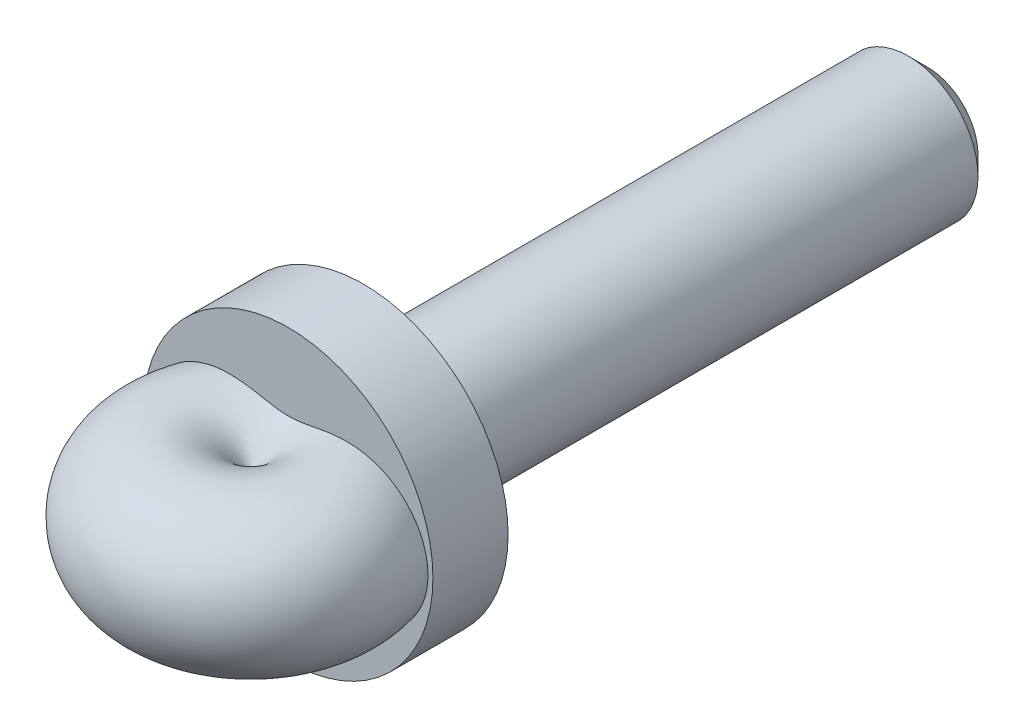
SolidWorks part; units mm, degrees
ref_plane "Front Plane" through (0, 0, 0) normal (0, 0, 1) x (1, 0, 0)
ref_plane "Top Plane" through (0, 0, 0) normal (0, 1, 0) x (1, 0, 0)
ref_plane "Right Plane" through (0, 0, 0) normal (1, 0, 0) x (0, 0, -1)
sketch "Sketch1" plane through (0, 0, 0) normal (0, 0, 1) x (1, 0, 0)
  circle A0 centre (0, 0) radius 4.699
  dimension "D1" = 9.398
extrude "Boss-Extrude1" add sketch "Sketch1" along normal blind 38.1
sketch "Sketch2" plane through (0, 0, 38.1) normal (0, 0, 1) x (1, 0, 0)
  circle A1 centre (0, 0) radius 9.779
  circle A2 centre (0, 0) radius 4.699
  circle A3 centre (0, 0) radius 4.699
  circle M3 centre (0, 0) radius 4.699
  dimension "D1" = 0
  dimension "D2" = 5.08
extrude "Boss-Extrude2" add sketch "Sketch2" along normal blind 5.08 contours M3 | A1 M3
ref_plane "Plane1" through (0, 0, 45.72) normal (0, 0, 1) x (1, 0, 0)
sketch "Sketch3" plane through (0, 0, 45.72) normal (0, 0, 1) x (1, 0, 0)
  line L0 (0, -1.9302) -> (0, 1.9302)
  arc A2 (0, -1.9302) -> (0, 1.9302) centre (4.699, 0) ccw
  circle A3 centre (0, 0) radius 9.779 construction
  point P7 (0, 0)
  point P10 (0, 0)
  dimension "D1" = 10.16
revolve "Revolve2" add sketch "Sketch3" angle 360 about L0
chamfer "Chamfer1" distance 1.27 angle 45 1 edges at (4.699, 0, 0)
sketch "Sketch4" plane through (0, 0, 38.1) normal (0, 0, -1) x (-1, 0, 0)
  circle A0 centre (0, 0) radius 4.699 construction
  circle A1 centre (0, 0) radius 9.779
  circle A2 centre (0, 0) radius 9.779
  circle A3 centre (0, 0) radius 4.699
  dimension "D1" = 0
extrude "Cut-Extrude1" cut sketch "Sketch4" along normal blind 9.398
